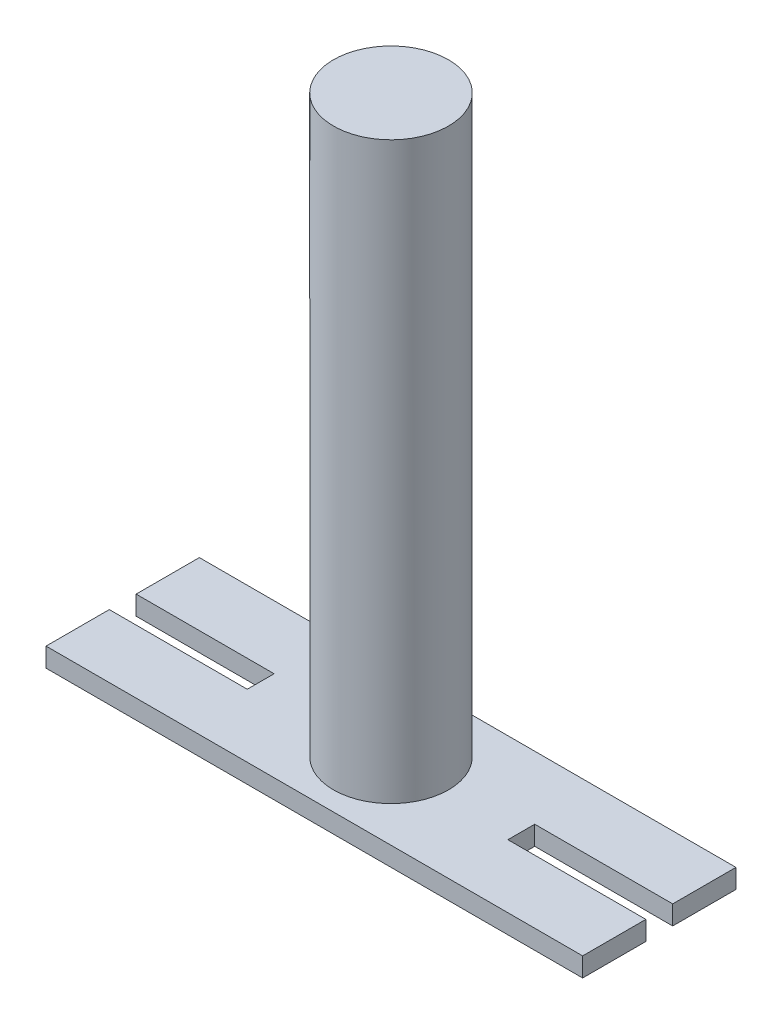
SolidWorks part; units mm, degrees
ref_plane "Front Plane" through (0, 0, 0) normal (0, 0, 1) x (1, 0, 0)
ref_plane "Top Plane" through (0, 0, 0) normal (0, 1, 0) x (1, 0, 0)
ref_plane "Right Plane" through (0, 0, 0) normal (1, 0, 0) x (0, 0, -1)
sketch "Sketch2" plane through (0, 0, 0) normal (0, 1, 0) x (1, 0, 0)
  line L0 (0, 508) -> (0, -508) construction
  line L1 (1778, 508) -> (-1778, 508)
  line L2 (1778, 508) -> (1778, 88.9)
  line L3 (1778, -508) -> (-1778, -508)
  line L4 (-1778, 508) -> (-1778, 88.9)
  line L5 (1778, 508) -> (-1778, -508) construction
  line L6 (1778, -508) -> (-1778, 508) construction
  line L7 (-1778, -88.9) -> (-863.6, -88.9)
  line L8 (-863.6, -88.9) -> (-863.6, 88.9)
  line L9 (-863.6, 0) -> (-1778, 0) construction
  line L10 (-1778, 88.9) -> (-863.6, 88.9)
  line L11 (1778, 88.9) -> (863.6, 88.9)
  line L12 (863.6, -88.9) -> (863.6, 88.9)
  line L13 (1778, -88.9) -> (863.6, -88.9)
  line L14 (-1778, -88.9) -> (-1778, -508)
  line L15 (1778, -88.9) -> (1778, -508)
  circle A0 centre (0, 0) radius 254
  point P0 (0, 0)
  point P20 (-1778, -1.1007)
  point P21 (0, 0)
  dimension "D3" = 508
  dimension "D1" = 3556
  dimension "D2" = 1016
  dimension "D4" = 419.1
  dimension "D5" = 914.4
extrude "Boss-Extrude1" add sketch "Sketch2" along normal blind 127 contours L15 L13 L12 L11 L2 L1 L4 L10 L8 L7 L14 L3 A0 | A0
sketch "Sketch3" plane through (0, 0, 0) normal (0, 0, 1) x (1, 0, 0)
  line L0 (0, 0) -> (0, 3937) construction
  line L1 (1778, 0) -> (-1778, 0) construction
  line L2 (0, 3937) -> (381, 3937)
  line L3 (381, 3937) -> (381, 127)
  line L4 (1778, 127) -> (-1778, 127) construction
  line L5 (381, 127) -> (254, 127)
  line L6 (254, 127) -> (254, 3810)
  line L7 (254, 3810) -> (0, 3810)
  line L8 (254, 0) -> (254, 127) construction
  line L9 (0, 3937) -> (0, 3810)
  dimension "D1" = 3937
  dimension "D2" = 381
  dimension "D3" = 3683
revolve "Revolve1" add sketch "Sketch3" angle 360 about L0
